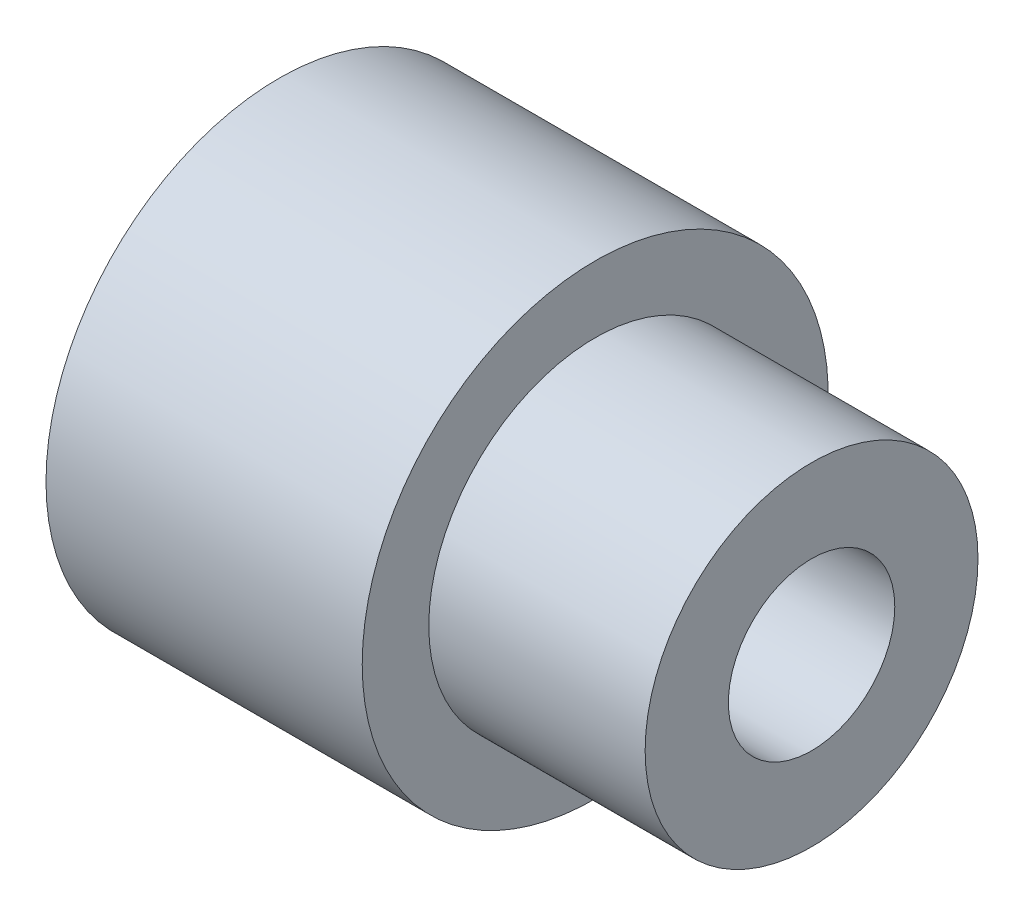
SolidWorks part; units mm, degrees
ref_plane "Front Plane" through (0, 0, 0) normal (0, 0, 1) x (1, 0, 0)
ref_plane "Top Plane" through (0, 0, 0) normal (0, 1, 0) x (1, 0, 0)
ref_plane "Right Plane" through (0, 0, 0) normal (1, 0, 0) x (0, 0, -1)
sketch "Sketch1" plane through (0, 0, 0) normal (1, 0, 0) x (0, 0, -1)
  circle A0 centre (0, 0) radius 10
  dimension "D1" = 20
extrude "Boss-Extrude1" add sketch "Sketch1" along normal blind 13
sketch "Sketch2" plane through (0, 0, 0) normal (-1, 0, 0) x (0, 0, 1)
  circle A0 centre (0, 0) radius 14
  dimension "D1" = 28
extrude "Boss-Extrude2" add sketch "Sketch2" along normal blind 19
sketch "Sketch3" plane through (-19, 0, 0) normal (-1, 0, 0) x (0, 0, 1)
  circle A0 centre (0, 0) radius 11
  dimension "D1" = 22
extrude "Cut-Extrude1" cut sketch "Sketch3" against normal blind 6
sketch "Sketch4" plane through (-13, 0, 0) normal (-1, 0, 0) x (0, 0, 1)
  circle A0 centre (0, 0) radius 9
  dimension "D1" = 18
extrude "Cut-Extrude2" cut sketch "Sketch4" against normal blind 10
sketch "Sketch5" plane through (13, 0, 0) normal (1, 0, 0) x (0, 0, -1)
  circle A0 centre (0, 0) radius 5
  dimension "D1" = 10
extrude "Cut-Extrude3" cut sketch "Sketch5" against normal through all
fillet "Fillet1" radius 0.05 1 edges at (-19, 0, 11)
